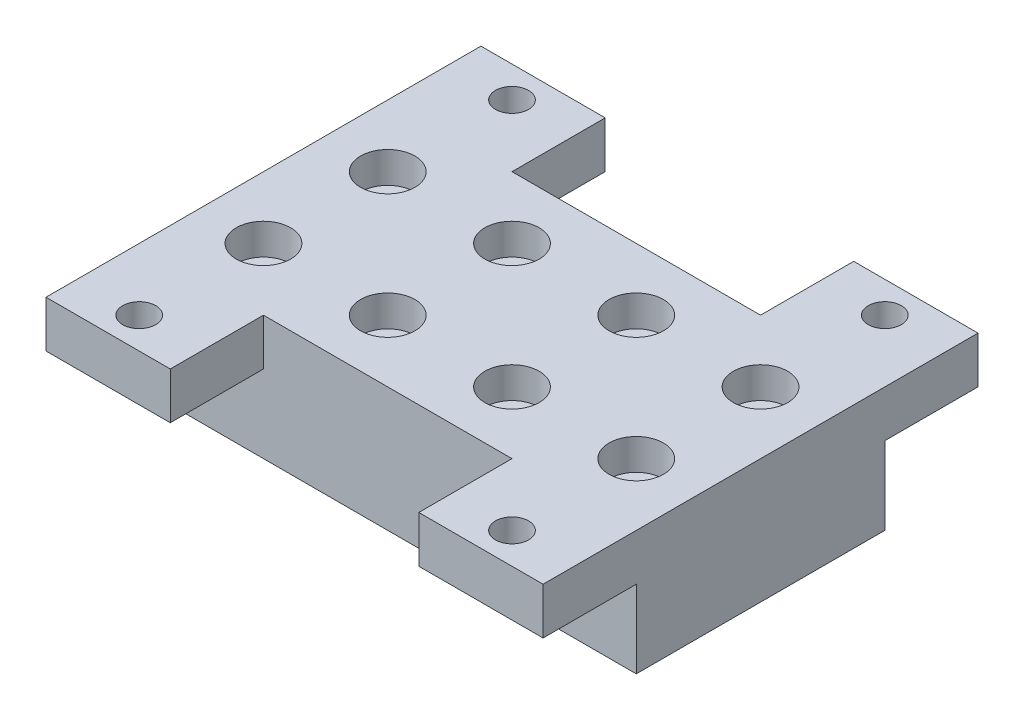
SolidWorks part; units mm, degrees
ref_plane "Front Plane" through (0, 0, 0) normal (0, 0, 1) x (1, 0, 0)
ref_plane "Top Plane" through (0, 0, 0) normal (0, 1, 0) x (1, 0, 0)
ref_plane "Right Plane" through (0, 0, 0) normal (1, 0, 0) x (0, 0, -1)
sketch "Sketch1" plane through (0, 0, 0) normal (0, 1, 0) x (1, 0, 0)
  line L1 (0, 0) -> (101.6, 0)
  line L2 (0, 0) -> (0, 50.8)
  line L3 (0, 50.8) -> (101.6, 50.8)
  line L4 (101.6, 0) -> (101.6, 50.8)
extrude "Boss-Extrude1" add sketch "Sketch1" along normal blind 25.4
hole_wizard "CBORE for 1/4 Socket Head Cap Screw1" positions "Sketch4" profile "Sketch3" counterbore size "1/4" standard "Ansi Inch" end condition through all
sketch "Sketch4" plane through (0, 25.4, 0) normal (0, 1, 0) x (-1, 0, 0)
  point P0 (-12.7, -12.7)
sketch "Sketch3" plane through (12.7, 25.4, -12.7) normal (1, 0, 0) x (0, 0, 1)
  line L0 (0, 0) -> (0, 25.4)
  line L1 (0, 25.4) -> (3.3782, 25.4)
  line L3 (3.3782, 25.4) -> (3.3782, 6.35)
  line L4 (3.3782, 6.35) -> (5.5562, 6.35)
  line L5 (5.5562, 6.35) -> (5.5563, 0)
  line L7 (5.5563, 0) -> (0, 0)
  line L11 (0, -6.35) -> (0, 107.95) construction
  dimension "Thru Hole Dia." = 6.7564
  dimension "Thru Hole Depth" = 25.4
  dimension "C'Bore Dia." = 11.1125
  dimension "C'Bore Depth" = 6.35
pattern_linear "LPattern1" count 2 spacing 25.4 along (0, 0, -1) count 4 spacing 25.4 along (1, 0, 0) of "CBORE for 1/4 Socket Head Cap Screw1"
hole_wizard "1/4 Clearance Hole1" positions "Sketch6" profile "Sketch5" hole size "1/4" standard "Ansi Inch" end condition through all
sketch "Sketch6" plane through (0, 25.4, 0) normal (0, 1, 0) x (-1, 0, 0)
  point P0 (-12.7, -38.1)
sketch "Sketch5" plane through (12.7, 25.4, -38.1) normal (1, 0, 0) x (0, 0, 1)
  line L0 (0, 0) -> (0, 25.4)
  line L1 (0, 25.4) -> (3.3782, 25.4)
  line L2 (3.3782, 25.4) -> (3.3782, 0)
  line L5 (3.3782, 0) -> (0, 0)
  line L11 (0, -6.35) -> (0, 107.95) construction
  dimension "Thru Hole Dia." = 6.7564
  dimension "Thru Hole Depth" = 25.4
pattern_linear "LPattern2" count 4 spacing 25.4 along (-1, 0, 0) of "1/4 Clearance Hole1"
sketch "Sketch7" plane through (0, 0, -50.8) normal (0, 0, -1) x (-1, 0, 0)
  line L0 (0, 25.4) -> (0, 0) construction
  line L1 (-101.6, 25.4) -> (0, 25.4)
  line L2 (-101.6, 25.4) -> (-101.6, 15.875)
  line L3 (-101.6, 15.875) -> (0, 15.875)
  line L4 (0, 25.4) -> (0, 15.875)
extrude "Boss-Extrude2" add sketch "Sketch7" along normal blind 19.05
sketch "Sketch8" plane through (0, 0, -69.85) normal (0, 0, -1) x (-1, 0, 0)
  line L0 (0, 25.4) -> (-101.6, 25.4) construction
  line L1 (-76.2, 25.4) -> (-25.4, 25.4)
  line L2 (-76.2, 25.4) -> (-76.2, 15.875)
  line L3 (-76.2, 15.875) -> (-25.4, 15.875)
  line L4 (-25.4, 25.4) -> (-25.4, 15.875)
  line L5 (-101.6, 15.875) -> (0, 15.875) construction
pattern_linear "LPattern3" count 2 spacing 25.4 along (0, 0, 1) of "1/4 Clearance Hole1"
pattern_linear "LPattern4" count 2 spacing 76.2 along (1, 0, 0) of "LPattern3"
sketch "Sketch11" plane through (0, 0, 0) normal (0, 0, 1) x (1, 0, 0)
  line L0 (101.6, 25.4) -> (101.6, 0) construction
  line L1 (0, 25.4) -> (101.6, 25.4)
  line L2 (0, 25.4) -> (0, 15.875)
  line L3 (0, 15.875) -> (101.6, 15.875)
  line L4 (101.6, 25.4) -> (101.6, 15.875)
extrude "Boss-Extrude3" add sketch "Sketch11" along normal blind 19.05
extrude "Cut-Extrude1" cut sketch "Sketch8" against normal blind 19.05
sketch "Sketch12" plane through (0, 0, 19.05) normal (0, 0, 1) x (1, 0, 0)
  line L0 (101.6, 25.4) -> (0, 25.4) construction
  line L1 (76.2, 25.4) -> (25.4, 25.4)
  line L2 (76.2, 25.4) -> (76.2, 15.875)
  line L3 (76.2, 15.875) -> (25.4, 15.875)
  line L4 (25.4, 25.4) -> (25.4, 15.875)
  line L5 (0, 15.875) -> (101.6, 15.875) construction
extrude "Cut-Extrude2" cut sketch "Sketch12" against normal blind 19.05
pattern_linear "LPattern5" count 2 spacing 50.8 along (0, 0, 1) count 2 spacing 76.2 along (1, 0, 0) of "1/4 Clearance Hole1"
